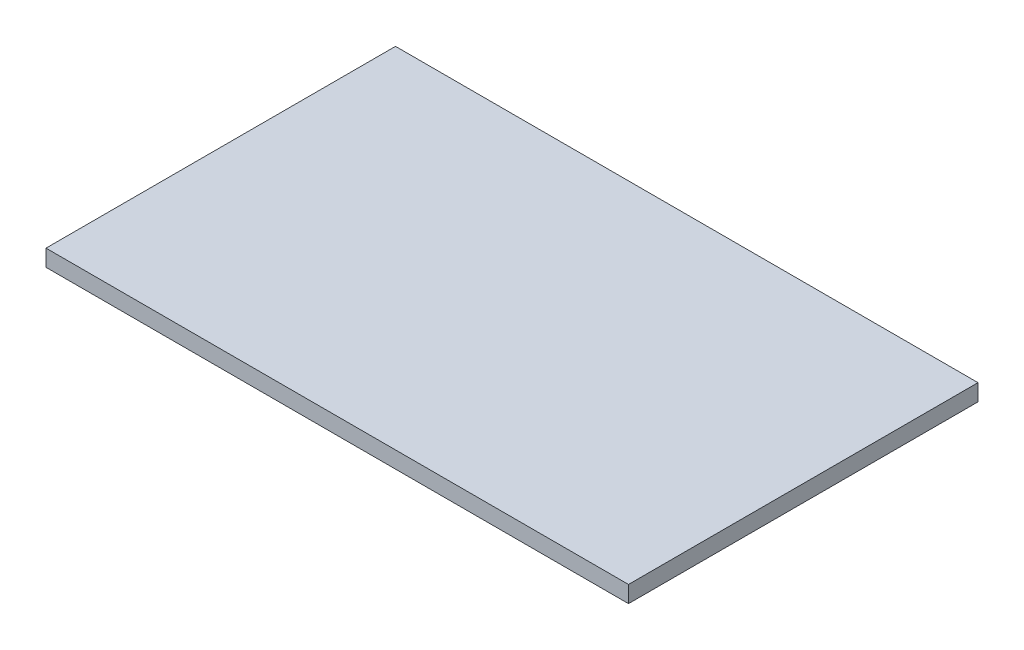
SolidWorks part; units mm, degrees
ref_plane "Face" through (0, 0, 0) normal (0, 0, 1) x (1, 0, 0)
ref_plane "Dessus" through (0, 0, 0) normal (0, 1, 0) x (1, 0, 0)
ref_plane "Droite" through (0, 0, 0) normal (1, 0, 0) x (0, 0, -1)
sketch "Esquisse1" plane through (0, 0, 0) normal (0, 1, 0) x (1, 0, 0)
  line L1 (0, 0) -> (350, 0)
  line L2 (0, 0) -> (0, 210)
  line L3 (0, 210) -> (350, 210)
  line L4 (350, 0) -> (350, 210)
  dimension "D1" = 210
  dimension "D2" = 350
extrude "Extrusion1" add sketch "Esquisse1" along normal blind 10
